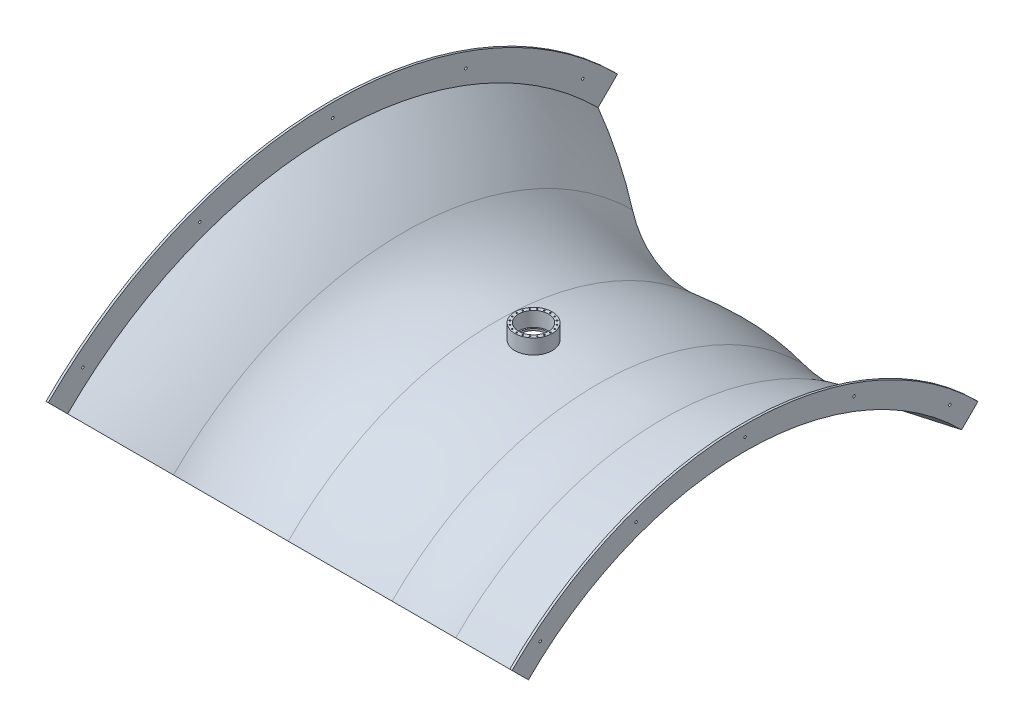
SolidWorks part; units mm, degrees
material "ABS"
ref_plane "Plano frontal" through (0, 0, 0) normal (0, 0, 1) x (1, 0, 0)
ref_plane "Plano superior" through (0, 0, 0) normal (0, 1, 0) x (1, 0, 0)
ref_plane "Plano direito" through (0, 0, 0) normal (1, 0, 0) x (0, 0, -1)
sketch "Esboço1" plane through (0, 0, 0) normal (0, 0, 1) x (1, 0, 0)
  line L0 (0, 0) -> (0, 3950) construction
  line L1 (0, 0) -> (8940.3328, 0) construction
  line L2 (2824, 4091) -> (1741, 3900)
  line L3 (2794, 4111.095) -> (1734.9585, 3924.3203)
  line L4 (2824, 4091) -> (2824, 4115.62)
  line L5 (2824, 4115.62) -> (2824, 4400)
  line L6 (-2710, 4997.3478) -> (-2710, 0) construction
  line L7 (2824, 4400) -> (2794, 4400)
  line L8 (2794, 4400) -> (2794, 4111.095)
  line L9 (2819.658, 4115.62) -> (1734.9585, 3924.3203) construction
  line L10 (2794, 4111.095) -> (2819.658, 4115.62) construction
  line L12 (2824, 4115.62) -> (2819.658, 4115.62) construction
  line L13 (-2710, 4997.3478) -> (-2710, 5375)
  line L14 (-2710, 5375) -> (-2680, 5375)
  line L15 (-2680, 5375) -> (-2680, 5008.9252)
  arc A0 (849.5312, 3857.5636) -> (1741, 3900) centre (1216.8727, 5525.5936) ccw
  arc A1 (849.5312, 3857.5636) -> (-483.402, 3920.309) centre (0, 0) ccw
  arc A2 (-1760, 4316) -> (-483.402, 3920.309) centre (-682.5146, 5535.0793) ccw
  arc A3 (854.9079, 3881.9785) -> (1734.9585, 3924.3203) centre (1216.8727, 5525.5936) ccw
  arc A4 (-1760, 4316) -> (-2710, 4997.3478) centre (-5575.2385, -0.6047) ccw
  arc A5 (854.9079, 3881.9785) -> (-486.4615, 3945.1211) centre (0, 0) ccw
  arc A6 (-1743.4437, 4334.732) -> (-486.4615, 3945.1211) centre (-682.5146, 5535.0793) ccw
  arc A7 (-1743.4437, 4334.732) -> (-2680, 5008.9252) centre (-5575.2385, -0.6047) ccw
  arc A10 (-1760, 4316) -> (-3771.6142, 5470.7809) centre (-5575.2385, -0.6047) ccw construction
  arc A11 (-1743.4437, 4334.732) -> (-3763.7873, 5494.5241) centre (-5575.2385, -0.6047) ccw construction
  point P14 (-1760, 4316)
  dimension "D3" = 3416
  dimension "D4" = 3950
  dimension "D7" = 3254
  dimension "D8" = 5761
  dimension "D1" = 4091
  dimension "D2" = 3900
  dimension "D5" = 2824
  dimension "D6" = 1741
  dimension "D9" = 2710
  dimension "D10" = 10750
  dimension "D11" = 1760
  dimension "D12" = 4316
  dimension "D14" = 4400
  dimension "D15" = 30
  dimension "D18" = 30
  dimension "D13" = 25
revolve "Revolução1" add sketch "Esboço1" angle 45 about L1
sketch "Esboço2" plane through (0, 0, 0) normal (0, 1, 0) x (1, 0, 0)
  circle A0 centre (0, 0) radius 180
  dimension "D1" = 360
extrude "Corte-extrusão1" cut sketch "Esboço2" along normal through all
sketch "Esboço3" plane through (0, 0, 0) normal (0, 1, 0) x (1, 0, 0)
  line L0 (-250, 0) -> (250, 0) construction
  line L1 (200, 0) -> (250, 0) construction
  circle A0 centre (0, 0) radius 200
  circle A1 centre (0, 0) radius 250
  dimension "D1" = 400
  dimension "D2" = 500
extrude "Ressalto-extrusão1" add sketch "Esboço3" against normal up to surface (196.0346 mm away) from offset 4166
hole_wizard "Broca de rosquear para tarraxa de M20x2.01" positions "Esboço5" profile "Esboço4" hole size "M20x2.0" standard "DIN"
sketch "Esboço5" plane through (0, 4166, 0) normal (0, 1, 0) x (1, 0, 0)
  line L0 (0, 200) -> (0, 250) construction
  circle A0 centre (0, 0) radius 200 construction
  circle A1 centre (0, 0) radius 200 construction
  circle A2 centre (0, 0) radius 250 construction
  point P0 (0, 225)
  point P14 (0, 225)
  point P21 (69.5288, 213.9877)
  point P22 (132.2517, 182.0288)
  point P23 (182.0288, 132.2517)
  point P24 (213.9877, 69.5288)
  point P25 (225, 0)
  point P26 (213.9877, -69.5288)
  point P27 (182.0288, -132.2517)
  point P28 (132.2517, -182.0288)
  point P29 (69.5288, -213.9877)
  point P30 (0, -225)
  point P31 (-69.5288, -213.9877)
  point P32 (-132.2517, -182.0288)
  point P33 (-182.0288, -132.2517)
  point P34 (-213.9877, -69.5288)
  point P35 (-225, 0)
  point P36 (-213.9877, 69.5288)
  point P37 (-182.0288, 132.2517)
  point P38 (-132.2517, 182.0288)
  point P39 (-69.5288, 213.9877)
  point P40 (0, 0)
  dimension "D1" = 20
sketch "Esboço4" plane through (0, 4166, -225) normal (1, 0, 0) x (0, 0, 1)
  line L0 (0, 0) -> (0, 57.4077)
  line L1 (0, 57.4077) -> (9, 52)
  line L2 (9, 52) -> (9, 0)
  line L5 (9, 0) -> (0, 0)
  line L10 (0, 57.4077) -> (-9, 52) construction
  line L11 (0, -6.35) -> (0, 107.95) construction
  dimension "Hole Dia." = 18
  dimension "Hole Depth" = 52
  dimension "Drill Angle" = 118
scale "Escala1" scale about origin uniform scaling yes scale factor 0.2
hole_wizard "Furo com folga de M62" positions "Esboço11" profile "Esboço12" hole size "M6" standard "Ansi Metric"
sketch "Esboço11" plane through (-536, 0, 0) normal (1, 0, 0) x (0, 0, -1)
  line L0 (0, 1001.785) -> (0, 1075) construction
  circle A2 centre (0, 0) radius 1038.3925 construction
  point P0 (0, 1038.3925)
  point P24 (355.1512, 975.7698)
  point P25 (667.4658, 795.4548)
  point P30 (-355.1512, 975.7698)
  point P31 (-667.4658, 795.4548)
sketch "Esboço12" plane through (-536, 1038.3925, 0) normal (0, 1, 0) x (0, 0, -1)
  line L0 (0, 0) -> (0, 17.9818)
  line L1 (0, 17.9818) -> (3.3, 15.999)
  line L2 (3.3, 15.999) -> (3.3, 0)
  line L3 (3.3, 0) -> (0, 0)
  line L4 (0, 17.9818) -> (-3.3, 15.999) construction
  line L5 (0, -6.35) -> (0, 107.95) construction
  dimension "Hole Dia." = 6.6
  dimension "Hole Depth" = 15.999
  dimension "Drill Angle" = 118
hole_wizard "Furo com folga de M63" positions "Esboço13" profile "Esboço14" hole size "M6" standard "Ansi Metric"
sketch "Esboço13" plane through (558.8, 0, 0) normal (-1, 0, 0) x (0, 0, 1)
  line L1 (0, 880) -> (0, 822.219) construction
  circle A2 centre (0, 0) radius 851.1095 construction
  point P0 (0, 851.1095)
  point P21 (291.0966, 799.7813)
  point P22 (547.0826, 651.9877)
  point P30 (-291.0966, 799.7813)
  point P31 (-547.0826, 651.9877)
sketch "Esboço14" plane through (558.8, 851.1095, 0) normal (0, 1, 0) x (0, 0, 1)
  line L0 (0, 0) -> (0, 17.9818)
  line L1 (0, 17.9818) -> (3.3, 15.999)
  line L2 (3.3, 15.999) -> (3.3, 0)
  line L3 (3.3, 0) -> (0, 0)
  line L4 (0, 17.9818) -> (-3.3, 15.999) construction
  line L5 (0, -6.35) -> (0, 107.95) construction
  dimension "Hole Dia." = 6.6
  dimension "Hole Depth" = 15.999
  dimension "Drill Angle" = 118
